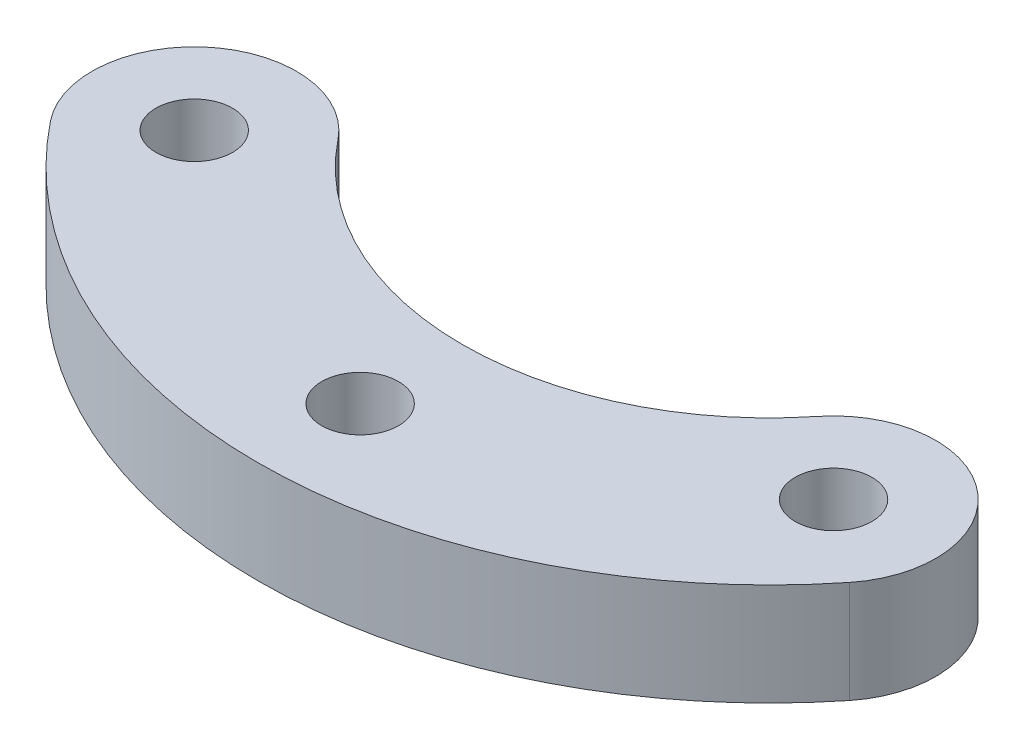
SolidWorks part; units mm, degrees
ref_plane "Front" through (0, 0, 0) normal (0, 0, 1) x (1, 0, 0)
ref_plane "Top" through (0, 0, 0) normal (0, 1, 0) x (1, 0, 0)
ref_plane "Right" through (0, 0, 0) normal (1, 0, 0) x (0, 0, -1)
sketch "Sketch1" plane through (0, 0, 0) normal (0, 1, 0) x (1, 0, 0)
  line L0 (-15.625, -12.4844) -> (-9.375, -7.4906) construction
  line L1 (9.375, -7.4906) -> (15.625, -12.4844) construction
  line L2 (0, -12) -> (0, -20) construction
  arc A0 (-9.375, -7.4906) -> (9.375, -7.4906) centre (0, 0) ccw
  arc A1 (-15.625, -12.4844) -> (15.625, -12.4844) centre (0, 0) ccw
  arc A2 (-15.625, -12.4844) -> (-9.375, -7.4906) centre (-12.5, -9.9875) cw
  arc A3 (9.375, -7.4906) -> (15.625, -12.4844) centre (12.5, -9.9875) cw
  circle A4 centre (-12.5, -9.9875) radius 1.5
  circle A5 centre (12.5, -9.9875) radius 1.5
  circle A6 centre (0, -16) radius 1.5
  dimension "D2" = 3
  dimension "D4" = 3
  dimension "D5" = 3
  dimension "D3" = 16
  dimension "D6" = 25
  dimension "D1" = 8
extrude "Boss-Extrude1" add sketch "Sketch1" along normal blind 4
equation "\"D4@Sketch1\"=\"D2@Sketch1\""
